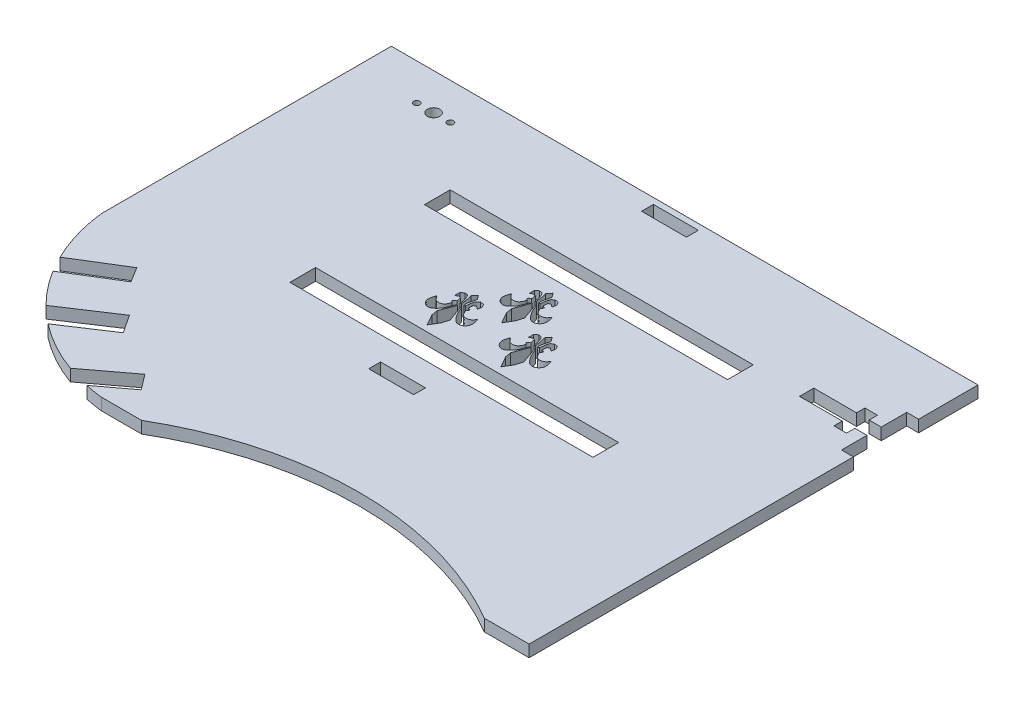
SolidWorks part; units mm, degrees
ref_plane "Front Plane" through (0, 0, 0) normal (0, 0, 1) x (1, 0, 0)
ref_plane "Top Plane" through (0, 0, 0) normal (0, 1, 0) x (1, 0, 0)
ref_plane "Right Plane" through (0, 0, 0) normal (1, 0, 0) x (0, 0, -1)
sketch "Sketch3" plane through (0, 0, 0) normal (0, 1, 0) x (1, 0, 0)
  line L1 (0, 0) -> (160, 0)
  line L2 (0, 0) -> (0, -120)
  line L3 (0, -120) -> (160, -120)
  line L4 (160, 0) -> (160, -120)
  dimension "D1" = 160
  dimension "D2" = 120
extrude "Boss-Extrude1" add sketch "Sketch3" along normal blind 3.175
sketch "Sketch4" plane through (0, 0, 0) normal (0, -1, 0) x (-1, 0, 0)
  line L0 (-160, -120) -> (-160, 0) construction
  line L1 (-160, -15.8763) -> (-156.825, -15.8763)
  line L2 (-160, -15.8763) -> (-160, -33.3114)
  line L3 (-160, -33.3114) -> (-156.825, -33.3114)
  line L4 (-156.825, -15.8763) -> (-156.825, -33.3114)
  dimension "D1" = 3.175
extrude "Cut-Extrude1" cut sketch "Sketch4" against normal through all
sketch "Sketch5" plane through (0, 0, 0) normal (0, -1, 0) x (1, 0, 0)
  line L0 (156.825, 26.4989) -> (156.825, 22.6889)
  line L1 (156.825, 33.3114) -> (156.825, 15.8763) construction
  line L2 (156.825, 24.5939) -> (156.825, 20.4537) construction
  line L3 (156.825, 24.5939) -> (150.221, 24.5939) construction
  line L4 (150.221, 20.4537) -> (150.221, 22.6889)
  line L5 (150.221, 20.4537) -> (153.5738, 20.4537)
  line L6 (153.5738, 20.4537) -> (153.5738, 22.6889)
  line L7 (153.5738, 22.6889) -> (156.825, 22.6889)
  line L8 (150.221, 22.6889) -> (138.791, 22.6889)
  line L9 (138.791, 22.6889) -> (138.791, 26.4989)
  line L10 (138.791, 24.5939) -> (156.825, 24.5939)
  line L11 (153.5738, 26.4989) -> (156.825, 26.4989)
  line L12 (153.5738, 28.7341) -> (153.5738, 26.4989)
  line L13 (150.221, 28.7341) -> (153.5738, 28.7341)
  line L14 (150.221, 28.7341) -> (150.221, 26.4989)
  line L15 (150.221, 26.4989) -> (138.791, 26.4989)
  dimension "D1" = 1.905
  dimension "D2" = 4.1402
  dimension "D3" = 6.604
  dimension "D4" = 11.43
  dimension "D5" = 1.905
  dimension "D6" = 3.2512
extrude "Cut-Extrude2" cut sketch "Sketch5" against normal through all contours L8 L9 L15 L14 L13 L12 L11 L0 L7 L6 L5 L4
sketch "Sketch6" plane through (0, 3.175, 0) normal (0, 1, 0) x (1, 0, 0)
  line L0 (160, 0) -> (0, 0) construction
  line L1 (90, -4.7651) -> (78, -4.7651)
  line L2 (90, -4.7651) -> (90, -1.5901)
  line L3 (90, -1.5901) -> (78, -1.5901)
  line L4 (78, -4.7651) -> (78, -1.5901)
  line L5 (160, -15.8763) -> (160, 0) construction
  dimension "D1" = 3.175
  dimension "D2" = 12
  dimension "D3" = 1.5901
  dimension "D4" = 70
extrude "Cut-Extrude3" cut sketch "Sketch6" against normal through all
sketch "Sketch8" plane through (0, 3.175, 0) normal (0, 1, 0) x (1, 0, 0)
  line L0 (0, -120) -> (160, -120) construction
  line L1 (0, 0) -> (3.17, 0)
  line L2 (0, 0) -> (0, -120)
  line L3 (0, -120) -> (3.17, -120)
  line L4 (3.17, 0) -> (3.17, -120)
  dimension "D1" = 3.17
extrude "Cut-Extrude4" cut sketch "Sketch8" against normal through all
sketch "Sketch10" plane through (0, 3.175, 0) normal (0, 1, 0) x (1, 0, 0)
  line L1 (78, -1.5901) -> (74.825, -1.5901)
  line L2 (78, -1.5901) -> (78, -4.7651)
  line L3 (78, -4.7651) -> (74.825, -4.7651)
  line L4 (74.825, -1.5901) -> (74.825, -4.7651)
  dimension "D1" = 3.175
extrude "Cut-Extrude6" cut sketch "Sketch10" against normal blind 3.175
sketch "Sketch9" plane through (0, 3.175, 0) normal (0, 1, 0) x (1, 0, 0)
  line L1 (90, -1.5901) -> (93.175, -1.5901)
  line L2 (90, -1.5901) -> (90, -4.7651)
  line L3 (90, -4.7651) -> (93.175, -4.7651)
  line L4 (93.175, -1.5901) -> (93.175, -4.7651)
  dimension "D1" = 3.175
sketch "Sketch11" plane through (90, 0, 0) normal (-1, 0, 0) x (0, 0, 1)
  line L0 (4.7651, 0) -> (1.5901, 0) construction
  line L1 (4.7651, 3.175) -> (1.5901, 3.175)
  line L2 (4.7651, 3.175) -> (4.7651, 0)
  line L3 (4.7651, 0) -> (1.5901, 0)
  line L4 (1.5901, 3.175) -> (1.5901, 0)
extrude "Boss-Extrude2" add sketch "Sketch11" along normal blind 3.175
sketch "Sketch12" plane through (0, 3.175, 0) normal (0, 1, 0) x (1, 0, 0)
  line L0 (3.17, 0) -> (33.17, 0) construction
  line L1 (160, 0) -> (3.17, 0) construction
  line L2 (33.17, 0) -> (33.17, -2.6213) construction
  line L3 (33.17, -2.6213) -> (33.17, -27.0604) construction
  line L4 (33.17, -27.0604) -> (20.6285, -27.0604) construction
  line L5 (20.6285, -27.0604) -> (20.6285, -2.6213) construction
  line L6 (20.6285, -2.6213) -> (33.17, -2.6213) construction
  line L8 (33.17, -27.0604) -> (20.6285, -27.0604)
  line L9 (33.17, -27.0604) -> (33.17, -2.6213)
  line L10 (33.17, -2.6213) -> (20.6285, -2.6213)
  line L11 (20.6285, -27.0604) -> (20.6285, -2.6213)
sketch "Sketch14" plane through (0, 3.175, 0) normal (0, 1, 0) x (1, 0, 0)
  line L0 (74.825, -4.7651) -> (74.825, -77.7115) construction
  line L1 (86.825, -4.7651) -> (86.825, -77.7115) construction
  line L3 (86.825, -77.7115) -> (74.825, -77.7115)
  line L4 (86.825, -77.7115) -> (86.825, -74.5315)
  line L5 (86.825, -74.5315) -> (74.825, -74.5315)
  line L6 (74.825, -77.7115) -> (74.825, -74.5315)
  dimension "D1" = 12
  dimension "D2" = 3.18
sketch "Sketch15" plane through (0, 3.175, 0) normal (0, 1, 0) x (1, 0, 0)
extrude "Cut-Extrude8" cut sketch "Sketch14" against normal through all
sketch "Sketch18" plane through (0, 3.175, 0) normal (0, 1, 0) x (1, 0, 0)
  line L0 (3.17, -120) -> (160, -120) construction
  line L1 (3.17, -120) -> (3.17, 0) construction
  arc A0 (56.7827, -120) -> (3.17, -77.5423) centre (51.2052, -71.9648) cw
extrude "Cut-Extrude9" cut sketch "Sketch18" against normal through all and the other way through all
sketch "Sketch20" plane through (0, 3.175, 0) normal (0, 1, 0) x (1, 0, 0)
  line L0 (10.0112, -97.2936) -> (22.9209, -89.3559)
  line L1 (10.0112, -97.2936) -> (7.5163, -93.2359)
  line L2 (22.9209, -89.3559) -> (20.426, -85.2982)
  line L3 (7.5163, -93.2359) -> (20.426, -85.2982)
  line L4 (17.011, -106.159) -> (30.4525, -97.2936)
  line L5 (17.011, -106.159) -> (20.229, -111.038)
  line L6 (30.4525, -97.2936) -> (33.6705, -102.1726)
  line L7 (20.229, -111.038) -> (33.6705, -102.1726)
  line L8 (34.8067, -117.4574) -> (46.1893, -108.8868)
  line L9 (34.8067, -117.4574) -> (37.8915, -121.5544)
  line L10 (46.1893, -108.8868) -> (49.2741, -112.9838)
  line L11 (37.8915, -121.5544) -> (49.2741, -112.9838)
  arc A0 (3.17, -77.5423) -> (45.6277, -120) centre (51.2052, -71.9648) ccw construction
  dimension "D1" = 12.9097
  dimension "D2" = 15.1548
  dimension "D3" = 4.7634
extrude "Cut-Extrude10" cut sketch "Sketch20" against normal blind 3.18
sketch "Sketch21" plane through (0, 3.175, 0) normal (0, 1, 0) x (1, 0, 0)
  line L2 (45.6277, -120) -> (160, -120) construction
  arc A0 (148.0334, -120) -> (56.4165, -120) centre (102.225, -198.2331) ccw
extrude "Cut-Extrude11" cut sketch "Sketch21" against normal blind 3.18
sketch "Sketch22" plane through (0, 3.175, 0) normal (0, 1, 0) x (1, 0, 0)
  line L1 (125.3057, -68.2257) -> (44.2802, -68.2257)
  line L2 (125.3057, -68.2257) -> (125.3057, -61.367)
  line L3 (125.3057, -61.367) -> (44.2802, -61.367)
  line L4 (44.2802, -68.2257) -> (44.2802, -61.367)
  line L5 (44.2802, -25.3917) -> (125.3057, -25.3917)
  line L6 (44.2802, -25.3917) -> (44.2802, -32.2517)
  line L7 (44.2802, -32.2517) -> (125.3057, -32.2517)
  line L8 (125.3057, -25.3917) -> (125.3057, -32.2517)
  dimension "D1" = 6.8587
  dimension "D2" = 6.86
extrude "Cut-Extrude12" cut sketch "Sketch22" against normal blind 3.18
sketch "Sketch23" plane through (0, 3.175, 0) normal (0, 1, 0) x (1, 0, 0)
  line L0 (92.0404, -59.5916) -> (90.3502, -56.6012)
  line L1 (90.3502, -56.6012) -> (90.0901, -55.0085)
  line L2 (90.0901, -55.0085) -> (91.5528, -51.0104)
  line L3 (86.5471, -51.6605) -> (86.6771, -51.628)
  line L4 (90.1551, -51.0104) -> (89.7326, -50.5878)
  line L5 (90.4802, -50.0352) -> (90.2527, -48.8325)
  line L6 (88.8874, -49.2226) -> (88.92, -47.6949)
  line L7 (88.92, -47.6949) -> (89.7001, -47.1098)
  line L8 (91.4553, -50.1652) -> (91.7154, -50.0352)
  line L9 (91.1628, -46.9473) -> (92.0404, -45.8746)
  line L10 (92.0404, -45.8746) -> (92.8855, -46.9798)
  line L11 (92.463, -50.1652) -> (92.7555, -50.0352)
  line L12 (93.8932, -47.1423) -> (94.8033, -47.2723)
  line L13 (95.0959, -49.2226) -> (94.3483, -48.67)
  line L14 (94.3483, -48.67) -> (93.7632, -48.9301)
  line L15 (93.7632, -48.9301) -> (93.6657, -50.1652)
  line L16 (93.6657, -50.1652) -> (94.2833, -50.3928)
  line L17 (92.723, -51.0104) -> (92.4955, -51.1404)
  line L18 (92.4955, -51.1404) -> (93.9907, -55.3985)
  line L19 (93.9907, -55.3985) -> (93.4056, -57.3163)
  line L20 (93.4056, -57.3163) -> (92.0404, -59.5916)
  line L21 (72.4725, -59.7439) -> (70.7822, -56.7534)
  line L22 (70.7822, -56.7534) -> (70.5222, -55.1607)
  line L23 (70.5222, -55.1607) -> (71.9849, -51.1626)
  line L24 (66.9791, -51.8127) -> (67.1092, -51.7802)
  line L25 (70.5872, -51.1626) -> (70.1646, -50.74)
  line L26 (70.9122, -50.1874) -> (70.6847, -48.9848)
  line L27 (69.3195, -49.3748) -> (69.352, -47.8471)
  line L28 (69.352, -47.8471) -> (70.1321, -47.262)
  line L29 (71.8874, -50.3175) -> (72.1474, -50.1874)
  line L30 (71.5948, -47.0995) -> (72.4725, -46.0268)
  line L31 (72.4725, -46.0268) -> (73.3176, -47.132)
  line L32 (72.895, -50.3175) -> (73.1876, -50.1874)
  line L33 (74.3252, -47.2945) -> (75.2354, -47.4245)
  line L34 (75.5279, -49.3748) -> (74.7803, -48.8222)
  line L35 (74.7803, -48.8222) -> (74.1952, -49.0823)
  line L36 (74.1952, -49.0823) -> (74.0977, -50.3175)
  line L37 (74.0977, -50.3175) -> (74.7153, -50.545)
  line L38 (73.1551, -51.1626) -> (72.9275, -51.2926)
  line L39 (72.9275, -51.2926) -> (74.4227, -55.5507)
  line L40 (74.4227, -55.5507) -> (73.8377, -57.4685)
  line L41 (73.8377, -57.4685) -> (72.4725, -59.7439)
  line L42 (81.9652, -49.2876) -> (80.275, -46.2972)
  line L43 (80.275, -46.2972) -> (80.0149, -44.7045)
  line L44 (80.0149, -44.7045) -> (81.4776, -40.7064)
  line L45 (76.4719, -41.3565) -> (76.6019, -41.324)
  line L46 (80.0799, -40.7064) -> (79.6574, -40.2838)
  line L47 (80.405, -39.7312) -> (80.1774, -38.5286)
  line L48 (78.8122, -38.9186) -> (78.8447, -37.3909)
  line L49 (78.8447, -37.3909) -> (79.6249, -36.8058)
  line L50 (81.3801, -39.8612) -> (81.6402, -39.7312)
  line L51 (81.0876, -36.6433) -> (81.9652, -35.5706)
  line L52 (81.9652, -35.5706) -> (82.8103, -36.6758)
  line L53 (82.3878, -39.8612) -> (82.6803, -39.7312)
  line L54 (83.818, -36.8383) -> (84.7281, -36.9683)
  line L55 (85.0207, -38.9186) -> (84.2731, -38.366)
  line L56 (84.2731, -38.366) -> (83.688, -38.6261)
  line L57 (83.688, -38.6261) -> (83.5905, -39.8612)
  line L58 (83.5905, -39.8612) -> (84.208, -40.0888)
  line L59 (82.6478, -40.7064) -> (82.4203, -40.8364)
  line L60 (82.4203, -40.8364) -> (83.9155, -45.0945)
  line L61 (83.9155, -45.0945) -> (83.3304, -47.0123)
  line L62 (83.3304, -47.0123) -> (81.9652, -49.2876)
  spline S0 degree 3 poles (91.5528, -51.0104) (91.4337, -51.0645) (91.2563, -51.057) (91.1953, -51.1729) (90.8083, -51.9082) (90.6898, -52.7741) (90.2527, -53.4807) (89.8857, -54.074) (89.3925, -54.6065) (88.8224, -55.0085) (88.5132, -55.2265) (88.089, -55.3396) (87.7173, -55.2685) (87.292, -55.1872) (86.8826, -54.924) (86.6121, -54.5859) (86.3316, -54.2353) (86.167, -53.7671) (86.157, -53.3182) (86.1444, -52.7507) (86.4171, -52.213) (86.5471, -51.6605) knots 0 0 0 0 1 1 1 2 2 2 3 3 3 4 4 4 5 5 5 6 6 6 7 7 7 7
  spline S1 degree 3 poles (86.6771, -51.628) (87.0022, -51.9855) (87.2213, -52.482) (87.6523, -52.7006) (88.0296, -52.892) (88.518, -52.8976) (88.92, -52.7656) (89.2996, -52.641) (89.6001, -52.3123) (89.8301, -51.9855) (90.0273, -51.7053) (90.0468, -51.3354) (90.1551, -51.0104) knots 0 0 0 0 1 1 1 2 2 2 3 3 3 4 4 4 4
  spline S2 degree 3 poles (89.7326, -50.5878) (89.8518, -50.4469) (89.9417, -50.2749) (90.0901, -50.1652) (90.2003, -50.0838) (90.3502, -50.0786) (90.4802, -50.0352) knots 0 0 0 0 1 1 1 2 2 2 2
  spline S3 degree 3 poles (90.2527, -48.8325) (90.0034, -48.8) (89.7467, -48.666) (89.505, -48.735) (89.2528, -48.8071) (89.0933, -49.0601) (88.8874, -49.2226) knots 0 0 0 0 1 1 1 2 2 2 2
  spline S4 degree 3 poles (89.7001, -47.1098) (89.9709, -47.1748) (90.3157, -47.1078) (90.5127, -47.3048) (90.8485, -47.6406) (91.0142, -48.1215) (91.1628, -48.5725) (91.3317, -49.0852) (91.3578, -49.6343) (91.4553, -50.1652) knots 0 0 0 0 1 1 1 2 2 2 3 3 3 3
  spline S5 degree 3 poles (91.7154, -50.0352) (91.6395, -49.4501) (91.5918, -48.8607) (91.4878, -48.28) (91.4073, -47.8299) (91.2711, -47.3915) (91.1628, -46.9473) knots 0 0 0 0 1 1 1 2 2 2 2
  spline S6 degree 3 poles (92.8855, -46.9798) (92.7772, -47.4457) (92.6719, -47.9123) (92.5605, -48.3775) (92.4877, -48.6816) (92.35, -48.9754) (92.333, -49.2876) (92.3169, -49.5829) (92.4196, -49.8727) (92.463, -50.1652) knots 0 0 0 0 1 1 1 2 2 2 3 3 3 3
  spline S7 degree 3 poles (92.7555, -50.0352) (92.8855, -49.3093) (92.8757, -48.5437) (93.1456, -47.8574) (93.2718, -47.5365) (93.644, -47.3807) (93.8932, -47.1423) knots 0 0 0 0 1 1 1 2 2 2 2
  spline S8 degree 3 poles (94.8033, -47.2723) (94.955, -47.5649) (95.2095, -47.8241) (95.2584, -48.1499) (95.312, -48.5076) (95.15, -48.865) (95.0959, -49.2226) knots 0 0 0 0 1 1 1 2 2 2 2
  spline S9 degree 3 poles (94.2833, -50.3928) (94.2291, -50.5661) (94.2072, -50.7531) (94.1207, -50.9128) (94.0623, -51.0206) (93.9474, -51.0862) (93.8607, -51.1729) knots 0 0 0 0 1 1 1 2 2 2 2
  spline S10 degree 3 poles (93.8607, -51.1729) (94.1532, -51.628) (94.329, -52.1843) (94.7383, -52.5381) (95.0108, -52.7736) (95.4185, -52.8421) (95.7785, -52.8306) (96.1347, -52.8193) (96.4921, -52.6745) (96.7861, -52.4731) (97.0964, -52.2605) (97.2845, -51.9097) (97.5337, -51.628) knots 0 0 0 0 1 1 1 2 2 2 3 3 3 4 4 4 4
  spline S11 degree 3 poles (97.5337, -51.628) (97.6638, -52.2347) (97.9502, -52.8283) (97.9238, -53.4482) (97.9048, -53.8946) (97.7108, -54.3589) (97.4037, -54.6834) (97.0973, -55.0072) (96.6454, -55.232) (96.201, -55.2685) (95.7913, -55.3022) (95.3461, -55.1424) (95.0309, -54.8784) (94.4458, -54.3884) (93.9917, -53.746) (93.6006, -53.0907) (93.215, -52.4443) (93.0156, -51.7038) (92.723, -51.0104) knots 0 0 0 0 1 1 1 2 2 2 3 3 3 4 4 4 5 5 5 6 6 6 6
  spline S12 degree 3 poles (71.9849, -51.1626) (71.8657, -51.2168) (71.6883, -51.2093) (71.6273, -51.3251) (71.2403, -52.0605) (71.1219, -52.9263) (70.6847, -53.633) (70.3177, -54.2262) (69.8246, -54.7587) (69.2545, -55.1607) (68.9452, -55.3788) (68.521, -55.4918) (68.1493, -55.4207) (67.724, -55.3394) (67.3146, -55.0762) (67.0442, -54.7381) (66.7637, -54.3875) (66.5991, -53.9193) (66.5891, -53.4704) (66.5765, -52.9029) (66.8491, -52.3653) (66.9791, -51.8127) knots 0 0 0 0 1 1 1 2 2 2 3 3 3 4 4 4 5 5 5 6 6 6 7 7 7 7
  spline S13 degree 3 poles (67.1092, -51.7802) (67.4342, -52.1377) (67.6534, -52.6342) (68.0843, -52.8528) (68.4617, -53.0442) (68.95, -53.0498) (69.352, -52.9178) (69.7316, -52.7932) (70.0322, -52.4645) (70.2621, -52.1377) (70.4593, -51.8575) (70.4788, -51.4876) (70.5872, -51.1626) knots 0 0 0 0 1 1 1 2 2 2 3 3 3 4 4 4 4
  spline S14 degree 3 poles (70.1646, -50.74) (70.2838, -50.5992) (70.3738, -50.4271) (70.5222, -50.3175) (70.6324, -50.236) (70.7822, -50.2308) (70.9122, -50.1874) knots 0 0 0 0 1 1 1 2 2 2 2
  spline S15 degree 3 poles (70.6847, -48.9848) (70.4355, -48.9523) (70.1787, -48.8182) (69.9371, -48.8873) (69.6849, -48.9593) (69.5254, -49.2123) (69.3195, -49.3748) knots 0 0 0 0 1 1 1 2 2 2 2
  spline S16 degree 3 poles (70.1321, -47.262) (70.403, -47.327) (70.7478, -47.2601) (70.9447, -47.457) (71.2805, -47.7928) (71.4462, -48.2737) (71.5948, -48.7247) (71.7638, -49.2374) (71.7899, -49.7866) (71.8874, -50.3175) knots 0 0 0 0 1 1 1 2 2 2 3 3 3 3
  spline S17 degree 3 poles (72.1474, -50.1874) (72.0716, -49.6024) (72.0238, -49.0129) (71.9199, -48.4322) (71.8393, -47.9821) (71.7032, -47.5437) (71.5948, -47.0995) knots 0 0 0 0 1 1 1 2 2 2 2
  spline S18 degree 3 poles (73.3176, -47.132) (73.2092, -47.5979) (73.1039, -48.0645) (72.9925, -48.5297) (72.9197, -48.8338) (72.782, -49.1276) (72.765, -49.4398) (72.7489, -49.7351) (72.8517, -50.0249) (72.895, -50.3175) knots 0 0 0 0 1 1 1 2 2 2 3 3 3 3
  spline S19 degree 3 poles (73.1876, -50.1874) (73.3176, -49.4615) (73.3077, -48.6959) (73.5776, -48.0096) (73.7038, -47.6887) (74.076, -47.5329) (74.3252, -47.2945) knots 0 0 0 0 1 1 1 2 2 2 2
  spline S20 degree 3 poles (75.2354, -47.4245) (75.3871, -47.7171) (75.6416, -47.9763) (75.6904, -48.3022) (75.7441, -48.6598) (75.5821, -49.0173) (75.5279, -49.3748) knots 0 0 0 0 1 1 1 2 2 2 2
  spline S21 degree 3 poles (74.7153, -50.545) (74.6611, -50.7184) (74.6393, -50.9054) (74.5528, -51.0651) (74.4944, -51.1729) (74.3794, -51.2384) (74.2927, -51.3251) knots 0 0 0 0 1 1 1 2 2 2 2
  spline S22 degree 3 poles (74.2927, -51.3251) (74.5853, -51.7802) (74.7611, -52.3365) (75.1704, -52.6903) (75.4428, -52.9258) (75.8505, -52.9943) (76.2105, -52.9829) (76.5667, -52.9715) (76.9242, -52.8268) (77.2182, -52.6253) (77.5284, -52.4127) (77.7166, -52.0619) (77.9658, -51.7802) knots 0 0 0 0 1 1 1 2 2 2 3 3 3 4 4 4 4
  spline S23 degree 3 poles (77.9658, -51.7802) (78.0958, -52.3869) (78.3822, -52.9805) (78.3558, -53.6005) (78.3368, -54.0468) (78.1428, -54.5112) (77.8358, -54.8356) (77.5293, -55.1594) (77.0774, -55.3842) (76.6331, -55.4207) (76.2233, -55.4544) (75.7781, -55.2947) (75.4629, -55.0307) (74.8778, -54.5407) (74.4237, -53.8983) (74.0327, -53.2429) (73.6471, -52.5966) (73.4476, -51.856) (73.1551, -51.1626) knots 0 0 0 0 1 1 1 2 2 2 3 3 3 4 4 4 5 5 5 6 6 6 6
  spline S24 degree 3 poles (81.4776, -40.7064) (81.3585, -40.7605) (81.1811, -40.753) (81.1201, -40.8689) (80.7331, -41.6042) (80.6146, -42.4701) (80.1774, -43.1767) (79.8104, -43.77) (79.3173, -44.3025) (78.7472, -44.7045) (78.4379, -44.9226) (78.0138, -45.0356) (77.6421, -44.9645) (77.2168, -44.8832) (76.8074, -44.62) (76.5369, -44.2819) (76.2564, -43.9313) (76.0918, -43.4631) (76.0818, -43.0142) (76.0692, -42.4467) (76.3419, -41.9091) (76.4719, -41.3565) knots 0 0 0 0 1 1 1 2 2 2 3 3 3 4 4 4 5 5 5 6 6 6 7 7 7 7
  spline S25 degree 3 poles (76.6019, -41.324) (76.927, -41.6815) (77.1461, -42.178) (77.5771, -42.3966) (77.9544, -42.588) (78.4427, -42.5936) (78.8447, -42.4616) (79.2244, -42.337) (79.5249, -42.0083) (79.7549, -41.6815) (79.9521, -41.4013) (79.9716, -41.0314) (80.0799, -40.7064) knots 0 0 0 0 1 1 1 2 2 2 3 3 3 4 4 4 4
  spline S26 degree 3 poles (79.6574, -40.2838) (79.7766, -40.143) (79.8665, -39.9709) (80.0149, -39.8612) (80.1251, -39.7798) (80.275, -39.7746) (80.405, -39.7312) knots 0 0 0 0 1 1 1 2 2 2 2
  spline S27 degree 3 poles (80.1774, -38.5286) (79.9282, -38.496) (79.6715, -38.362) (79.4298, -38.431) (79.1776, -38.5031) (79.0181, -38.7561) (78.8122, -38.9186) knots 0 0 0 0 1 1 1 2 2 2 2
  spline S28 degree 3 poles (79.6249, -36.8058) (79.8957, -36.8708) (80.2405, -36.8038) (80.4375, -37.0008) (80.7733, -37.3366) (80.9389, -37.8175) (81.0876, -38.2685) (81.2565, -38.7812) (81.2826, -39.3303) (81.3801, -39.8612) knots 0 0 0 0 1 1 1 2 2 2 3 3 3 3
  spline S29 degree 3 poles (81.6402, -39.7312) (81.5643, -39.1461) (81.5166, -38.5567) (81.4126, -37.976) (81.3321, -37.5259) (81.1959, -37.0875) (81.0876, -36.6433) knots 0 0 0 0 1 1 1 2 2 2 2
  spline S30 degree 3 poles (82.8103, -36.6758) (82.702, -37.1417) (82.5967, -37.6083) (82.4853, -38.0735) (82.4125, -38.3776) (82.2748, -38.6714) (82.2578, -38.9836) (82.2416, -39.2789) (82.3444, -39.5687) (82.3878, -39.8612) knots 0 0 0 0 1 1 1 2 2 2 3 3 3 3
  spline S31 degree 3 poles (82.6803, -39.7312) (82.8103, -39.0053) (82.8005, -38.2397) (83.0704, -37.5534) (83.1966, -37.2325) (83.5688, -37.0767) (83.818, -36.8383) knots 0 0 0 0 1 1 1 2 2 2 2
  spline S32 degree 3 poles (84.7281, -36.9683) (84.8798, -37.2609) (85.1343, -37.5201) (85.1832, -37.8459) (85.2368, -38.2036) (85.0748, -38.5611) (85.0207, -38.9186) knots 0 0 0 0 1 1 1 2 2 2 2
  spline S33 degree 3 poles (84.208, -40.0888) (84.1539, -40.2621) (84.132, -40.4492) (84.0455, -40.6089) (83.9871, -40.7166) (83.8722, -40.7822) (83.7855, -40.8689) knots 0 0 0 0 1 1 1 2 2 2 2
  spline S34 degree 3 poles (83.7855, -40.8689) (84.078, -41.324) (84.2538, -41.8803) (84.6631, -42.2341) (84.9356, -42.4696) (85.3433, -42.5381) (85.7033, -42.5266) (86.0595, -42.5153) (86.4169, -42.3705) (86.7109, -42.1691) (87.0212, -41.9565) (87.2093, -41.6057) (87.4585, -41.324) knots 0 0 0 0 1 1 1 2 2 2 3 3 3 4 4 4 4
  spline S35 degree 3 poles (87.4585, -41.324) (87.5885, -41.9307) (87.875, -42.5243) (87.8486, -43.1442) (87.8296, -43.5906) (87.6356, -44.055) (87.3285, -44.3794) (87.0221, -44.7032) (86.5701, -44.928) (86.1258, -44.9645) (85.7161, -44.9982) (85.2709, -44.8384) (84.9557, -44.5744) (84.3706, -44.0845) (83.9165, -43.4421) (83.5254, -42.7867) (83.1398, -42.1404) (82.9404, -41.3998) (82.6478, -40.7064) knots 0 0 0 0 1 1 1 2 2 2 3 3 3 4 4 4 5 5 5 6 6 6 6
extrude "Cut-Extrude13" cut sketch "Sketch23" against normal blind 3.18
sketch "Sketch24" plane through (0, 3.175, 0) normal (0, 1, 0) x (1, 0, 0)
  line L0 (25.2149, 0) -> (25.2149, -9.77) construction
  line L1 (160, 0) -> (3.17, 0) construction
  line L2 (19.7251, -9.77) -> (28.7251, -9.77) construction
  circle A0 centre (28.7251, -9.77) radius 0.83
  circle A1 centre (19.7251, -9.77) radius 0.83
  dimension "D1" = 9.77
  dimension "D2" = 9
extrude "Cut-Extrude14" cut sketch "Sketch24" against normal blind 10
sketch "Sketch25" plane through (0, 3.175, 0) normal (0, 1, 0) x (1, 0, 0)
  line L0 (74.825, -1.5901) -> (3.17, -1.5901) construction
  line L1 (3.17, -77.5423) -> (3.17, 0) construction
  line L2 (28.7251, -9.77) -> (19.7251, -9.77) construction
  line L3 (74.825, -4.7651) -> (3.17, -4.7651) construction
  line L4 (24.2251, -9.77) -> (24.2251, -4.7651) construction
  circle A0 centre (24.2251, -9.77) radius 1.656
  dimension "D1" = 5.0049
extrude "Cut-Extrude15" cut sketch "Sketch25" against normal blind 80.772
